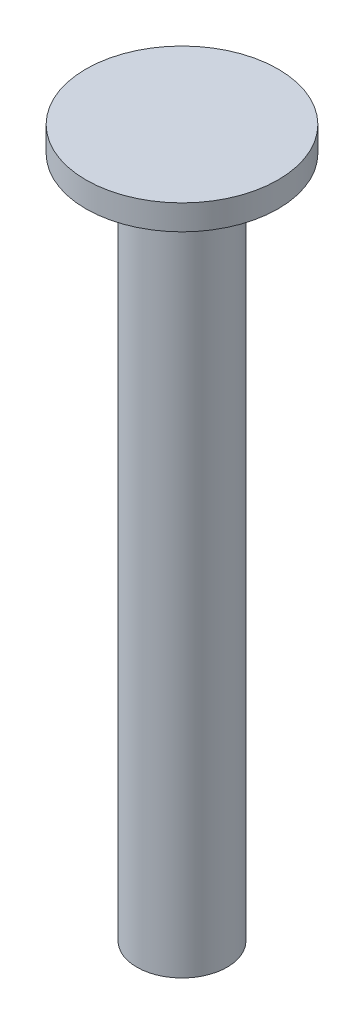
SolidWorks part; units mm, degrees
ref_plane "Front Plane" through (0, 0, 0) normal (0, 0, 1) x (1, 0, 0)
ref_plane "Top Plane" through (0, 0, 0) normal (0, 1, 0) x (1, 0, 0)
ref_plane "Right Plane" through (0, 0, 0) normal (1, 0, 0) x (0, 0, -1)
sketch "Sketch2" plane through (0, -47.6664, 0) normal (0, 1, 0) x (1, 0, 0)
  line L0 (3.8482, 5.6112) -> (50003.8482, 5.6112) construction
  line L1 (5.0939, 6.8569) -> (5.0939, -49993.1431) construction
  circle A3 centre (8.1152, -1.319) radius 1.1441
extrude "Boss-Extrude1" add sketch "Sketch2" against normal up to vertex (17.27 mm away)
sketch "Sketch3" plane through (0, -47.6664, 0) normal (0, 1, 0) x (1, 0, 0)
  circle A0 centre (8.1152, -1.319) radius 2.4326
extrude "Boss-Extrude2" add sketch "Sketch3" along normal blind 0.635
